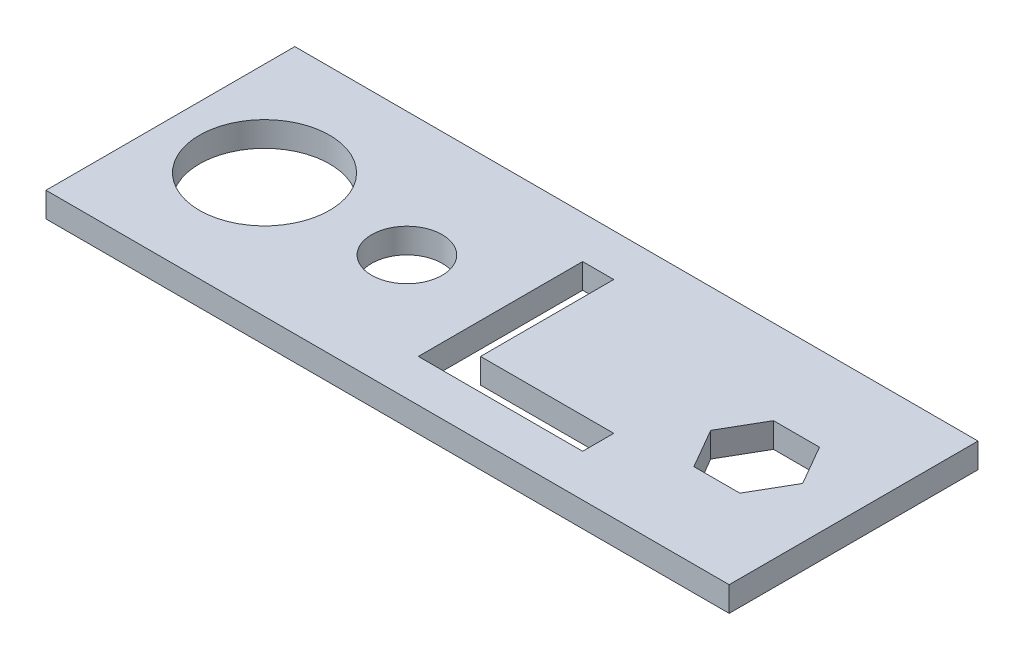
SolidWorks part; units mm, degrees
ref_plane "Front Plane" through (0, 0, 0) normal (0, 0, 1) x (1, 0, 0)
ref_plane "Top Plane" through (0, 0, 0) normal (0, 1, 0) x (1, 0, 0)
ref_plane "Right Plane" through (0, 0, 0) normal (1, 0, 0) x (0, 0, -1)
sketch "Sketch1" plane through (0, 0, 0) normal (0, 1, 0) x (1, 0, 0)
  line L0 (0, 15) -> (82.3633, 15) construction
  line L1 (0, 0) -> (82.3633, 0)
  line L2 (0, 0) -> (0, 30)
  line L3 (0, 30) -> (82.3633, 30)
  line L4 (82.3633, 0) -> (82.3633, 30)
  line L5 (39.7938, 24.905) -> (39.7938, 5.095)
  line L6 (39.7938, 5.095) -> (59.6038, 5.095)
  line L7 (59.6038, 5.095) -> (59.6038, 8.845)
  line L8 (59.6038, 8.845) -> (43.5438, 8.845)
  line L9 (43.5438, 8.845) -> (43.5438, 24.905)
  line L10 (43.5438, 24.905) -> (39.7938, 24.905)
  line L12 (73.4517, 19.8) -> (67.9091, 19.8)
  line L13 (67.9091, 19.8) -> (65.1379, 15)
  line L14 (65.1379, 15) -> (67.9091, 10.2)
  line L15 (67.9091, 10.2) -> (73.4517, 10.2)
  line L16 (73.4517, 10.2) -> (76.223, 15)
  line L17 (76.223, 15) -> (73.4517, 19.8)
  circle A0 centre (11.3456, 15) radius 7.85
  circle A1 centre (28.5118, 15) radius 4.25
  circle A2 centre (70.6804, 15) radius 4.8 construction
  point P17 (39.7938, 15)
  point P18 (75.4804, 15)
  point P19 (82.3633, 15)
  dimension "D3" = 15.7
  dimension "D4" = 8.5
  dimension "D2" = 30
  dimension "D5" = 3.75
  dimension "D6" = 19.81
  dimension "D7" = 9.6
extrude "Boss-Extrude1" add sketch "Sketch1" along normal blind 3
equation "\"8mm hole\" = 8.4mm'used to be the diameter of the linear motion rods"
equation "\"22mm hole\"= 23mm'this is the size of the hole for the nema 17 standard was 22mm"
equation "\"15mm hole\"= 15.8mm'this is the hole for the linear motion sliders, they are all set to this measurement so if you have different sized bearing sliders you may have to adjust individually"
equation "\"bed height offset\"= 3mm'this is how far the bed has been offset from a low point (probably don't want to edit, but can)"
equation "\"#10 nut width\"= 9.6mm'this is the width of a nut from flat side to other flat side"
equation "\"#10 bolt diameter\"= 5mm'This is the diameter including the threads"
equation "\"Al_width\"= 19.31mm'Self explainatory"
equation "\"Al_thick\"= 3.35mm"
equation "\"lin_rd_vert_hole_tol\"= 0.5mm"
equation "\"lin_rd_horz_hole_tol\"= 0.5mm"
equation "\"lin_rd_diam\"= 8mm"
equation "\"slid_diam\"= 15mm"
equation "\"slid_vert_tol\"= 0.7mm"
equation "\"mot_face_ridge_diam\"= 22mm"
equation "\"mot_face_ridge_tol\"= 1mm"
equation "\"slid_horz_tol\"= 0.8"
equation "\"Al_thick_tol\" = 0.4mm"
equation "\"Al_width_tol\" = 0.5mm"
equation "\"D3@Sketch1\"= \"slid_diam\" + \"slid_vert_tol\""
equation "\"D4@Sketch1\"= \"lin_rd_diam\" + \"lin_rd_vert_hole_tol\""
equation "\"D5@Sketch1\"= \"Al_thick\" + \"Al_thick_tol\""
equation "\"D6@Sketch1\"= \"Al_width\" + \"Al_width_tol\""
equation "\"D7@Sketch1\"= \"#10 nut width\""
